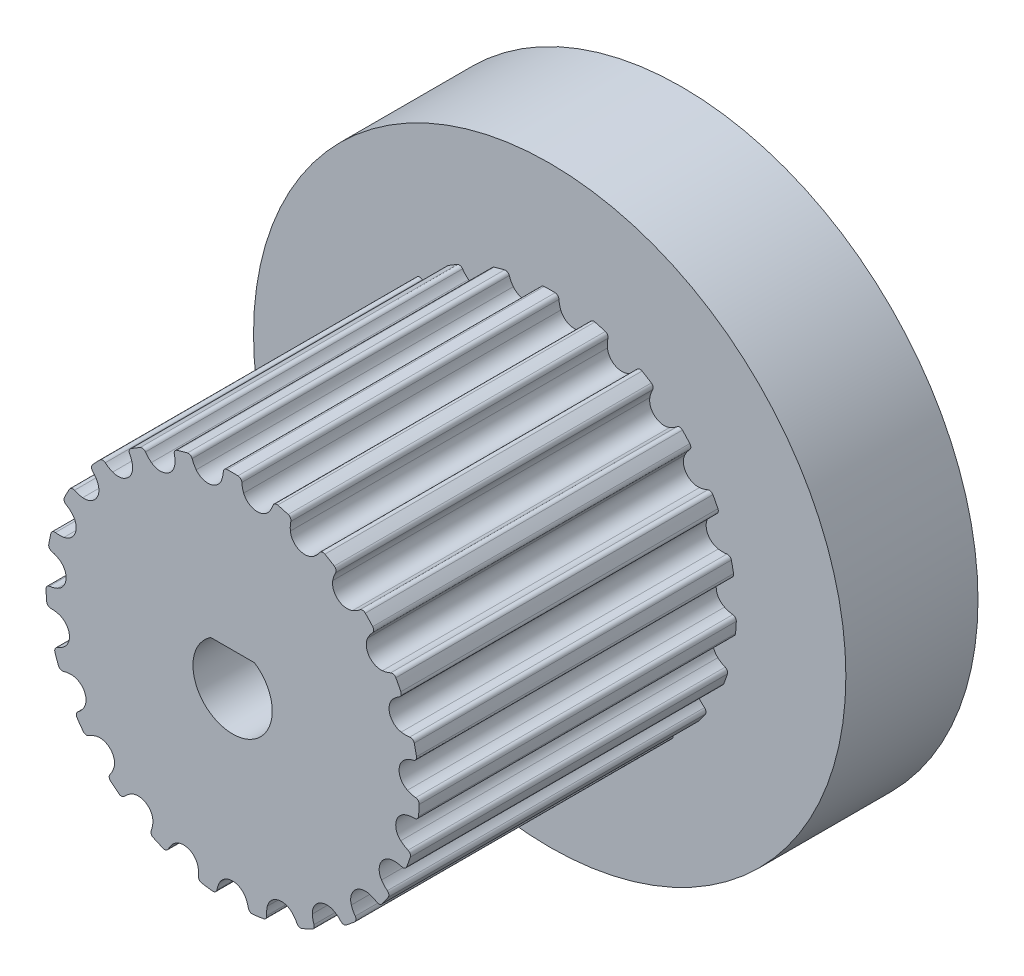
SolidWorks part; units mm, degrees
ref_plane "Front Plane" through (0, 0, 0) normal (0, 0, 1) x (1, 0, 0)
ref_plane "Top Plane" through (0, 0, 0) normal (0, 1, 0) x (1, 0, 0)
ref_plane "Right Plane" through (0, 0, 0) normal (1, 0, 0) x (0, 0, -1)
sketch "Sketch1" plane through (0, 0, 0) normal (0, 0, 1) x (1, 0, 0)
  line L0 (0, 0) -> (0, 50.6756) construction
  circle A4 centre (0, 0) radius 7.3211 construction
  circle A6 centre (0, 0) radius 7.0671
  dimension "D2" = 14.6423
  dimension "D1" = 0.254
extrude "Boss-Extrude1" add sketch "Sketch1" along normal blind 12
sketch "Sketch2" plane through (0, 0, 12) normal (0, 0, 1) x (1, 0, 0)
  line L0 (0, 0) -> (0, 7.0671) construction
  line L1 (0, 0) -> (0.9623, 7.0013) construction
  line L2 (0, 0) -> (1.3496, 6.9716) construction
  arc A0 (0.3509, 6.9217) -> (0.2054, 7.0641) centre (0.2011, 6.9142) ccw
  circle A3 centre (0, 0) radius 6.3171 construction
  arc A4 (0.4196, 6.6043) -> (1.3778, 6.4725) centre (0.9358, 6.8081) ccw
  arc A5 (0.3509, 6.9217) -> (0.4196, 6.6043) centre (1.3496, 6.9716) ccw
  circle A7 centre (0, 0) radius 7.0671 construction
  arc A8 (1.5296, 6.7597) -> (1.7081, 6.8576) centre (1.6718, 6.7121) cw
  arc A9 (1.5296, 6.7597) -> (1.3778, 6.4725) centre (0.5813, 7.0772) cw
  arc A10 (0.2054, 7.0641) -> (1.7081, 6.8576) centre (0, 0) cw
  dimension "D4" = 1.11
  dimension "D6" = 2
  dimension "D7" = 0.3
  dimension "D3" = 7.826
  dimension "D5" = 3.13
  dimension "D1" = 0.75
extrude "Cut-Extrude1" cut sketch "Sketch2" against normal through all
pattern_circular "CirPattern5" count 23 over 360 about axis through (0, 0, 0) along (0, 0, 1) of "Cut-Extrude1"
sketch "Croquis1" plane through (0, 0, 12) normal (0, 0, 1) x (1, 0, 0)
  line L0 (-0.8292, 1.25) -> (0.8292, 1.25)
  line L1 (0, -1.5) -> (0, 1.25) construction
  arc A0 (-0.8292, 1.25) -> (0.8292, 1.25) centre (0, 0) ccw
  point P1 (-0.8292, 1.25)
  dimension "D1" = 3
  dimension "D2" = 2.75
extrude "Cortar-Extruir1" cut sketch "Croquis1" against normal blind 6
sketch "Croquis2" plane through (0, 0, 0) normal (0, 0, -1) x (-1, 0, 0)
  circle A0 centre (0, 0) radius 11.2088
extrude "Saliente-Extruir1" add sketch "Croquis2" along normal blind 5
equation "\"Number_of_teeth\"= 23"
equation "\"D2@Sketch1\"=(\"Number_of_teeth\"*2)/PI"
equation "\"GT\"= 2"
equation "\"R\"= ( \"Number_of_teeth\" * 2 ) / PI"
equation "\"D3@Sketch2\"=180/(\"Number_of_teeth\")"
equation "\"D5@Sketch2\"=72/(\"Number_of_teeth\")"
equation "\"D1@CirPattern5\"=\"Number_of_teeth\""
